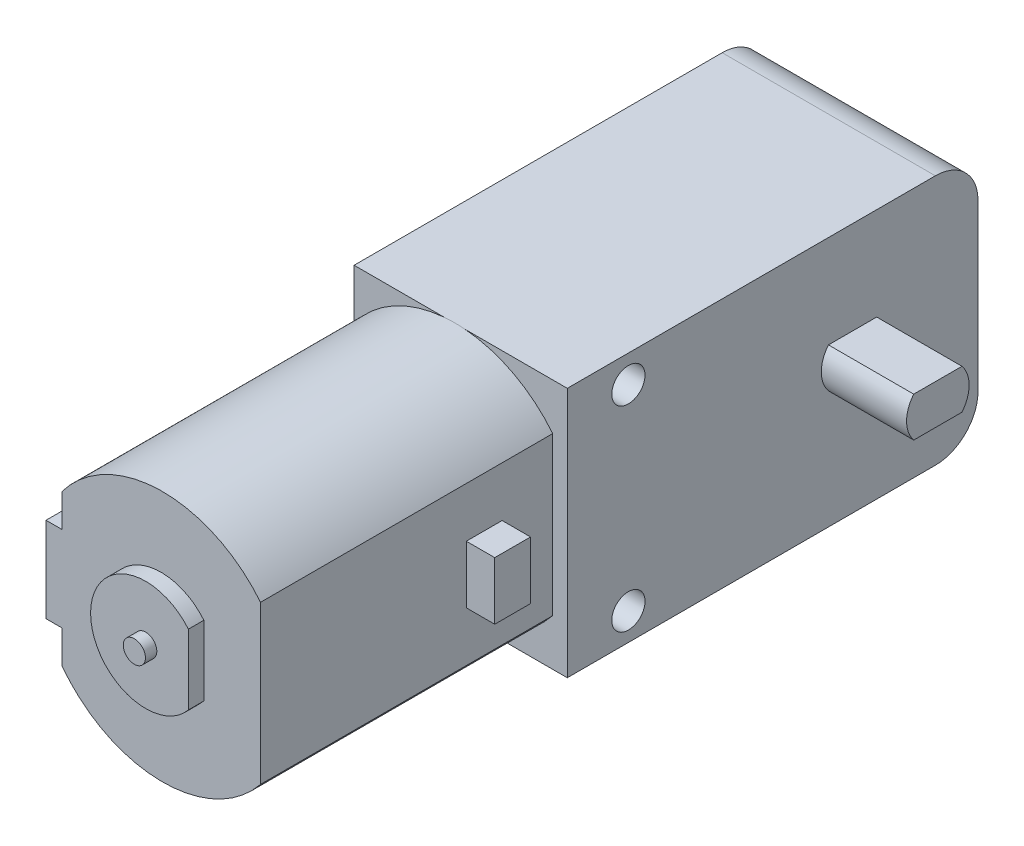
SolidWorks part; units mm, degrees
ref_plane "Front Plane" through (0, 0, 0) normal (0, 0, 1) x (1, 0, 0)
ref_plane "Top Plane" through (0, 0, 0) normal (0, 1, 0) x (1, 0, 0)
ref_plane "Right Plane" through (0, 0, 0) normal (1, 0, 0) x (0, 0, -1)
sketch "Sketch1" plane through (0, 0, 0) normal (0, 1, 0) x (1, 0, 0)
  line L1 (9.525, -18.3515) -> (-9.525, -18.3515)
  line L2 (9.525, -18.3515) -> (9.525, 18.3515)
  line L3 (9.525, 18.3515) -> (-9.525, 18.3515)
  line L4 (-9.525, -18.3515) -> (-9.525, 18.3515)
  line L5 (9.525, -18.3515) -> (-9.525, 18.3515) construction
  line L6 (9.525, 18.3515) -> (-9.525, -18.3515) construction
  point P0 (0, 0)
  dimension "D1" = 19.05
  dimension "D2" = 36.703
extrude "Boss-Extrude1" add sketch "Sketch1" along normal blind 22.4028
sketch "Sketch2" plane through (9.525, 0, 0) normal (1, 0, 0) x (0, 0, -1)
  line L0 (4.9873, 14.0928) -> (9.2978, 14.0928)
  line L5 (4.9873, 10.5368) -> (9.2978, 10.5368)
  circle A2 centre (7.1425, 12.3148) radius 2.794
  point P6 (7.1425, 12.3148)
  dimension "D2" = 1.778
  dimension "D1" = 5.588
  dimension "D3" = 1.778
extrude "Boss-Extrude2" add sketch "Sketch2" along normal blind 7.62 contours L0 A2 L5
sketch "Sketch3" plane through (9.525, 0, 0) normal (1, 0, 0) x (0, 0, -1)
  line L1 (-18.3515, 11.2014) -> (18.3515, 11.2014) construction
  line L2 (18.3515, 22.4028) -> (18.3515, 0) construction
  line L3 (-18.3515, 22.4028) -> (-18.3515, 0) construction
  circle A0 centre (-12.8905, 19.9517) radius 1.4859
  circle A2 centre (-12.8905, 2.4511) radius 1.4859
  dimension "D1" = 2.9718
  dimension "D2" = 8.7503
  dimension "D5" = 31.242
extrude "Cut-Extrude1" cut sketch "Sketch3" against normal through all
fillet "Fillet1" radius 3.81 2 edges at (0, 0, -18.3515) (0, 22.4028, -18.3515)
sketch "Sketch6" plane through (0, 0, -18.3515) normal (0, 0, -1) x (-1, 0, 0)
  line L1 (1.9939, 8.6868) -> (-0.9271, 8.6868)
  line L2 (1.9939, 8.6868) -> (1.9939, 13.716)
  line L3 (1.9939, 13.716) -> (-0.9271, 13.716)
  line L4 (-0.9271, 8.6868) -> (-0.9271, 13.716)
  line L5 (1.9939, 8.6868) -> (-0.9271, 13.716) construction
  line L6 (1.9939, 13.716) -> (-0.9271, 8.6868) construction
  point P5 (0, 0)
  point P6 (0, 0)
  point P7 (0, 0)
  dimension "D1" = 2.921
  dimension "D2" = 5.0292
extrude "Boss-Extrude3" add sketch "Sketch6" along normal blind 4.8006
fillet "Fillet2" radius 0.254 4 edges at (-0.5334, 8.6868, -18.3515) (-0.5334, 8.6868, -23.1521) (-0.5334, 13.716, -23.1521) (-0.5334, 13.716, -18.3515)
sketch "Sketch7" plane through (0.9271, 0, 0) normal (1, 0, 0) x (0, 0, -1)
  line L4 (23.1521, 8.9408) -> (23.1521, 13.462) construction
  circle A1 centre (20.7518, 11.2014) radius 1.4097
  point P5 (23.1521, 11.2014)
  dimension "D1" = 2.8194
extrude "Cut-Extrude2" cut sketch "Sketch7" against normal through all
sketch "Sketch8" plane through (0, 0, 18.3515) normal (0, 0, 1) x (1, 0, 0)
  line L0 (-9.525, 22.4028) -> (-9.525, 0) construction
  line L1 (-9.525, 17.9451) -> (-9.525, 4.4577)
  line L2 (8.2232, 4.1553) -> (8.2232, 18.2475)
  arc A0 (-9.525, 4.4577) -> (8.2232, 4.1553) centre (-0.5334, 11.2014) ccw
  arc A1 (8.2232, 18.2475) -> (-9.525, 17.9451) centre (-0.5334, 11.2014) ccw
  dimension "D1" = 22.479
  dimension "D2" = 8.9916
  dimension "D3" = 8.7566
extrude "Boss-Extrude4" add sketch "Sketch8" along normal blind 26.1112
sketch "Sketch11" plane through (-9.525, 0, 0) normal (-1, 0, 0) x (0, 0, 1)
  line L0 (44.4627, 17.9451) -> (44.4627, 4.4577) construction
  line L1 (22.8727, 13.7795) -> (26.0731, 13.7795)
  line L2 (22.8727, 13.7795) -> (22.8727, 8.6233)
  line L3 (22.8727, 8.6233) -> (26.0731, 8.6233)
  line L4 (26.0731, 13.7795) -> (26.0731, 8.6233)
  line L5 (22.8727, 13.7795) -> (26.0731, 8.6233) construction
  line L6 (22.8727, 8.6233) -> (26.0731, 13.7795) construction
  line L8 (-18.3515, 18.5928) -> (-18.3515, 3.81) construction
  point P0 (-18.3515, 11.2014)
  point P13 (24.4729, 11.2014)
  dimension "D1" = 21.59
  dimension "D2" = 5.1562
  dimension "D3" = 3.2004
extrude "Boss-Extrude5" add sketch "Sketch11" along normal blind 2.54
ref_plane "Plane1" through (-0.6509, 0, 0) normal (1, 0, 0) x (0, 0, -1)
mirror "Mirror1" about plane through (-0.6509, 0, 0) normal (1, 0, 0) of "Boss-Extrude5"
sketch "Sketch12" plane through (-9.525, 0, 0) normal (-1, 0, 0) x (0, 0, 1)
  line L0 (44.4627, 17.9451) -> (44.4627, 4.4577) construction
  line L1 (44.4627, 7.3914) -> (36.0045, 7.3914)
  line L2 (44.4627, 7.3914) -> (44.4627, 15.0114)
  line L3 (44.4627, 15.0114) -> (36.0045, 15.0114)
  line L4 (36.0045, 7.3914) -> (36.0045, 15.0114)
  point P6 (44.4627, 11.2014)
  point P7 (36.0045, 11.2014)
  dimension "D1" = 8.4582
  dimension "D2" = 7.62
extrude "Boss-Extrude6" add sketch "Sketch12" along normal blind 1.4224
sketch "Sketch13" plane through (0, 0, 44.4627) normal (0, 0, 1) x (1, 0, 0)
  line L0 (-0.6509, -12.3215) -> (-0.6509, 12.3215) construction
  line L1 (3.1591, 8.0765) -> (3.1591, 14.3263)
  arc A0 (3.1591, 14.3263) -> (3.1591, 8.0765) centre (-0.6509, 11.2014) ccw
  dimension "D1" = 9.8552
  dimension "D2" = 3.81
extrude "Boss-Extrude7" add sketch "Sketch13" along normal blind 1.3843
sketch "Sketch14" plane through (0, 0, 45.847) normal (0, 0, 1) x (1, 0, 0)
  circle A0 centre (-0.6509, 11.2014) radius 0.9906
  dimension "D1" = 1.9812
extrude "Boss-Extrude8" add sketch "Sketch14" along normal blind 1.016
